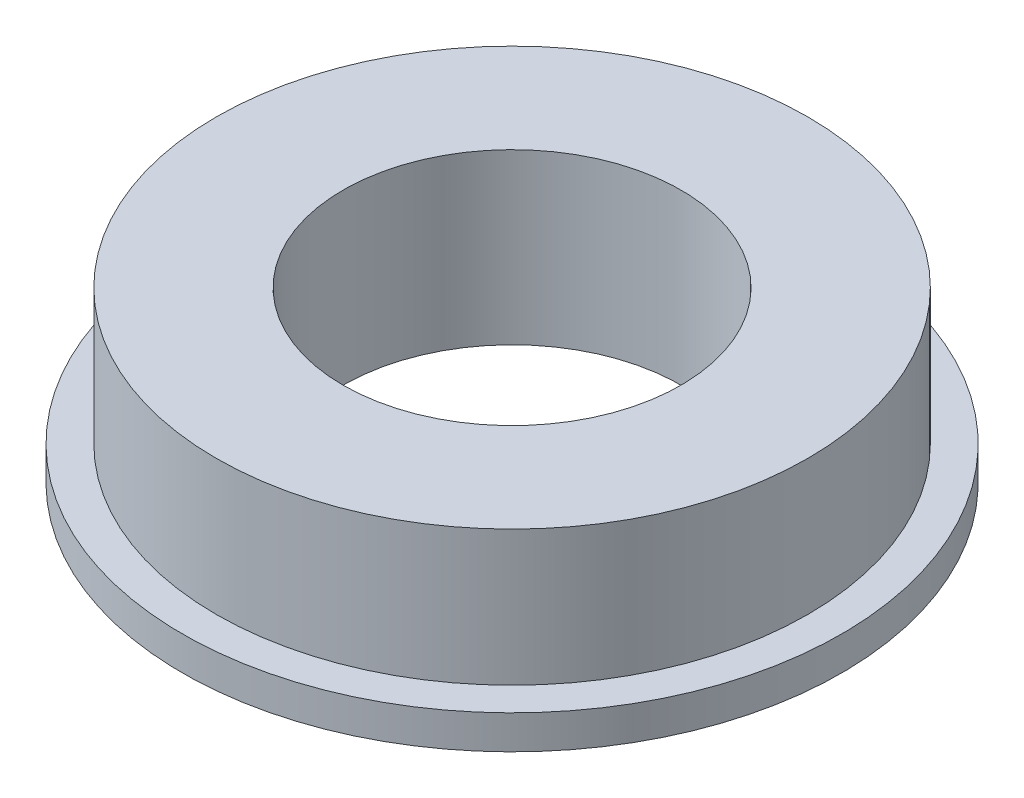
SolidWorks part; units mm, degrees
material "合金钢"
ref_plane "前视基准面" through (0, 0, 0) normal (0, 0, 1) x (1, 0, 0)
ref_plane "上视基准面" through (0, 0, 0) normal (0, 1, 0) x (1, 0, 0)
ref_plane "右视基准面" through (0, 0, 0) normal (1, 0, 0) x (0, 0, -1)
sketch "草图1" plane through (0, 0, 0) normal (0, 1, 0) x (1, 0, 0)
  circle A0 centre (0, 0) radius 7
  circle A1 centre (0, 0) radius 4
  dimension "D1" = 14
  dimension "D2" = 8
extrude "凸台-拉伸1" add sketch "草图1" along normal blind 4
sketch "草图2" plane through (0, 0, 0) normal (0, -1, 0) x (1, 0, 0)
  circle A0 centre (0, 0) radius 7.8
  circle A2 centre (0, 0) radius 4 construction
  circle A3 centre (0, 0) radius 4
  dimension "D1" = 15.6
extrude "凸台-拉伸2" add sketch "草图2" against normal blind 0.8
